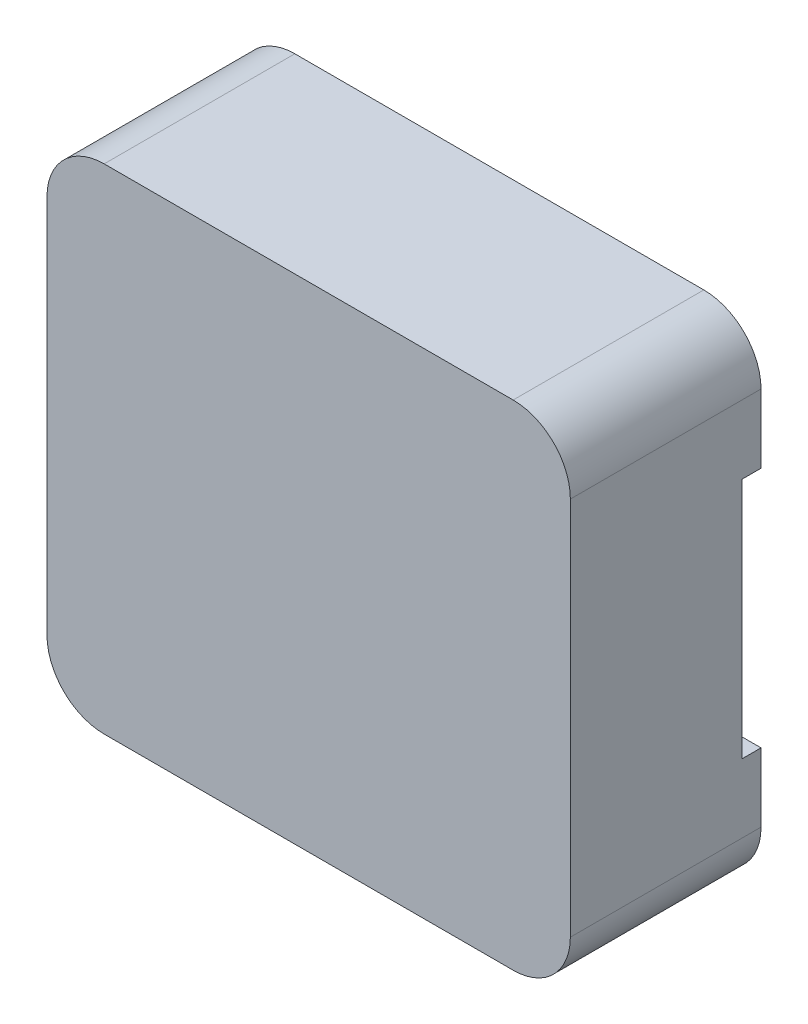
SolidWorks part; units mm, degrees
ref_plane "Plan de face" through (0, 0, 0) normal (0, 0, 1) x (1, 0, 0)
ref_plane "Plan de dessus" through (0, 0, 0) normal (0, 1, 0) x (1, 0, 0)
ref_plane "Plan de droite" through (0, 0, 0) normal (1, 0, 0) x (0, 0, -1)
sketch "Esquisse1" plane through (0, 0, 0) normal (0, 0, 1) x (1, 0, 0)
  line L1 (0, 0) -> (5.49, 0)
  line L2 (0, 0) -> (0, 5.18)
  line L3 (0, 5.18) -> (5.49, 5.18)
  line L4 (5.49, 0) -> (5.49, 5.18)
extrude "Boss.-Extru.1" add sketch "Esquisse1" along normal blind 2
fillet "Congé1" radius 0.6 4 edges at (0, 0, 1) (0, 5.18, 1) (5.49, 0, 1) (5.49, 5.18, 1)
sketch "Esquisse2" plane through (0, 0, 0) normal (0, 0, -1) x (-1, 0, 0)
  line L0 (0, 2.59) -> (-5.49, 2.59) construction
  line L1 (0, 4.58) -> (0, 0.6) construction
  line L2 (-5.49, 0.6) -> (-5.49, 4.58) construction
  line L3 (0, 3.86) -> (-1.02, 3.86)
  line L4 (0, 1.32) -> (-1.02, 1.32)
  line L7 (-4.47, 0.6) -> (-4.47, 4.58)
  line L8 (-4.47, 1.32) -> (-4.47, 3.86)
  line L9 (-4.47, 3.86) -> (-5.49, 3.86)
  line L10 (-1.02, 4.58) -> (-1.02, 0.6)
  line L11 (-1.02, 3.86) -> (-1.02, 1.32)
  line L12 (-4.47, 1.32) -> (-5.49, 1.32)
  line L13 (0, 3.86) -> (-5.49, 3.86) construction
  line L14 (-5.49, 3.86) -> (-5.49, 1.32)
  line L15 (0, 1.32) -> (-5.49, 1.32) construction
  line L16 (0, 3.86) -> (0, 1.32)
  dimension "D1" = 1.27
  dimension "D2" = 1.27
  dimension "D3" = 1.02
  dimension "D4" = 1.02
extrude "Enlèv. mat.-Extru.1" cut sketch "Esquisse2" against normal blind 0.2
